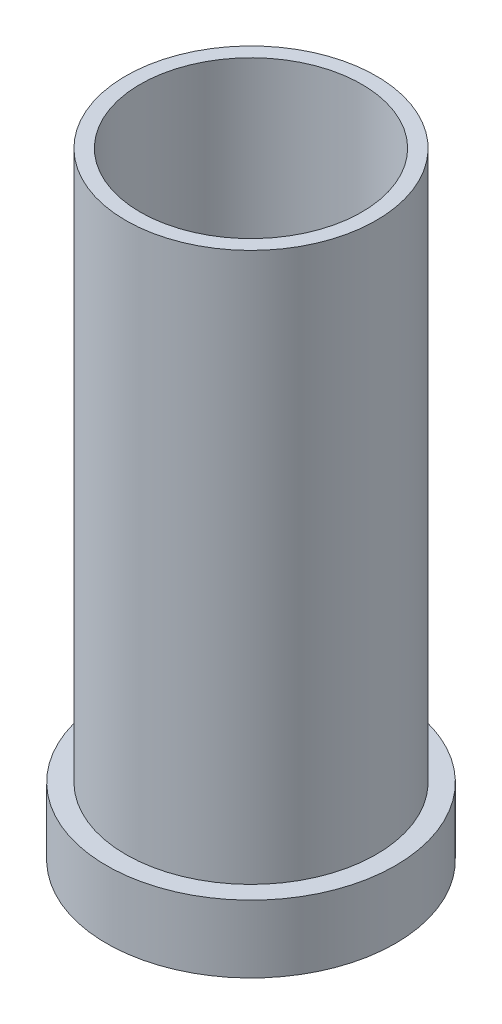
SolidWorks part; units mm, degrees
ref_plane "Front Plane" through (0, 0, 0) normal (0, 0, 1) x (1, 0, 0)
ref_plane "Top Plane" through (0, 0, 0) normal (0, 1, 0) x (1, 0, 0)
ref_plane "Right Plane" through (0, 0, 0) normal (1, 0, 0) x (0, 0, -1)
sketch "Sketch5" plane through (0, 0, 0) normal (0, 1, 0) x (1, 0, 0)
  circle A0 centre (0, 0) radius 5.5
  dimension "D1" = 11
extrude "Extrude-Thin5" add sketch "Sketch5" against normal blind 3.5 separate body thin
sketch "Sketch6" plane through (0, 0, 0) normal (0, 1, 0) x (1, 0, 0)
  circle A0 centre (0, 0) radius 6.5
extrude "Boss-Extrude1" add sketch "Sketch6" along normal blind 28.5
sketch "Sketch8" plane through (0, 28.5, 0) normal (0, 1, 0) x (1, 0, 0)
  circle A0 centre (0, 0) radius 1
hole_wizard "Ø11.5 (11.5) Diameter Hole1" positions "3DSketch1" profile "Sketch9" hole size "Ø11.5" standard "ANSI Metric"
sketch3d "3DSketch1"
  line L0 (0, 28.5, 0) -> (0, 0, 0) construction
  point P0 (0, 28.5, 0)
sketch "Sketch9" plane through (0, 28.5, 0) normal (1, 0, 0) x (0, 0, 1)
  line L0 (0, 0) -> (0, 22.093)
  line L1 (0, 22.093) -> (5.75, 18.5)
  line L2 (5.75, 18.5) -> (5.75, 0)
  line L5 (5.75, 0) -> (0, 0)
  line L10 (0, 22.093) -> (-5.75, 18.5) construction
  line L11 (0, -6.35) -> (0, 107.95) construction
  dimension "Hole Dia." = 11.5
  dimension "Hole Depth" = 18.5
  dimension "Drill Angle" = 116
sketch "Sketch14" plane through (0, -3.5, 0) normal (0, -1, 0) x (-1, 0, 0)
  circle A0 centre (0, 0) radius 1.5174
hole_wizard "Ø11.0 (11) Diameter Hole2" positions "3DSketch2" profile "Sketch17" hole size "Ø11.0" standard "ANSI Metric"
sketch3d "3DSketch2"
  point P0 (0, -3.5, 0)
sketch "Sketch17" plane through (0, -3.5, 0) normal (1, 0, 0) x (0, 0, -1)
  line L0 (0, 0) -> (0, 7.4368)
  line L1 (0, 7.4368) -> (5.5, 4)
  line L2 (5.5, 4) -> (5.5, 0)
  line L5 (5.5, 0) -> (0, 0)
  line L10 (0, 7.4368) -> (-5.5, 4) construction
  line L11 (0, -6.35) -> (0, 107.95) construction
  dimension "Hole Dia." = 11
  dimension "Hole Depth" = 4
  dimension "Drill Angle" = 116
equation "\"Base_H\"=104"
